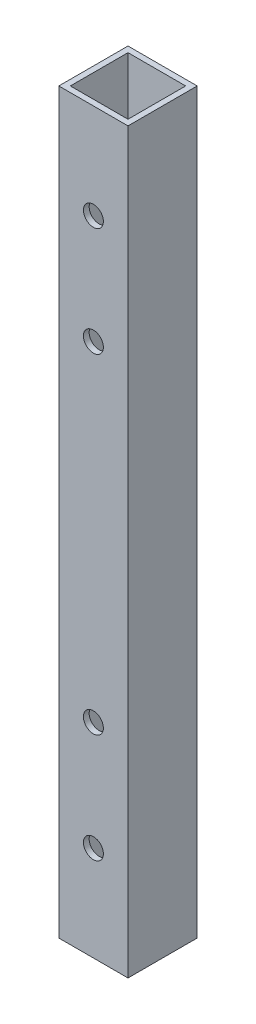
SolidWorks part; units mm, degrees
material "6063-T5"
ref_plane "Front Plane" through (0, 0, 0) normal (0, 0, 1) x (1, 0, 0)
ref_plane "Top Plane" through (0, 0, 0) normal (0, 1, 0) x (1, 0, 0)
ref_plane "Right Plane" through (0, 0, 0) normal (1, 0, 0) x (0, 0, -1)
sketch "Sketch1" plane through (0, 0, 0) normal (0, 1, 0) x (1, 0, 0)
  line L0 (1.5875, 1.5875) -> (17.4625, 1.5875)
  line L5 (0, 0) -> (19.05, 0)
  line L6 (0, 0) -> (0, 19.05)
  line L7 (0, 19.05) -> (19.05, 19.05)
  line L8 (19.05, 0) -> (19.05, 19.05)
  line L9 (17.4625, 1.5875) -> (17.4625, 17.4625)
  line L10 (1.5875, 17.4625) -> (17.4625, 17.4625)
  line L11 (1.5875, 1.5875) -> (1.5875, 17.4625)
  dimension "D1" = 19.05
  dimension "D2" = 19.05
  dimension "D3" = 1.5875
extrude "Boss-Extrude1" add sketch "Sketch1" along normal blind 914.4
sketch "Sketch2" plane through (0, 0, 0) normal (0, 0, 1) x (1, 0, 0)
  line L0 (0, 914.4) -> (19.05, 914.4) construction
  circle A0 centre (9.525, 906.4) radius 2.75
  circle A1 centre (9.525, 891.4) radius 2.75
  dimension "D3" = 5.5
  dimension "D4" = 5.5
  dimension "D1" = 8
  dimension "D2" = 15
extrude "Cut-Extrude1" cut sketch "Sketch2" against normal through all
sketch "Sketch3" plane through (0, 0, -19.05) normal (0, 0, -1) x (-1, 0, 0)
  circle A0 centre (-9.525, 906.4) radius 4.255
  circle A1 centre (-9.525, 891.4) radius 4.255
  dimension "D1" = 8.51
  dimension "D2" = 8.51
extrude "Cut-Extrude2" cut sketch "Sketch3" against normal up to next
sketch "Sketch4" plane through (0, 0, 0) normal (0, 0, 1) x (1, 0, 0)
  line L0 (0, 914.4) -> (0, 0) construction
  line L1 (0, 762) -> (19.05, 762)
  line L2 (0, 762) -> (0, 558.8)
  line L3 (0, 558.8) -> (19.05, 558.8)
  line L4 (19.05, 762) -> (19.05, 558.8)
  line L5 (19.05, 914.4) -> (19.05, 0) construction
  line L6 (0, 914.4) -> (19.05, 914.4) construction
  dimension "D1" = 152.4
  dimension "D2" = 203.2
extrude "Cut-Extrude3" cut sketch "Sketch4" against normal through all flip side to cut
sketch "Sketch5" plane through (0, 0, 0) normal (0, 0, 1) x (1, 0, 0)
  line L0 (19.05, 762) -> (0, 762) construction
  line L1 (19.05, 762) -> (19.05, 558.8) construction
  line L2 (0, 660.4) -> (19.05, 660.4) construction
  line L3 (0, 762) -> (0, 558.8) construction
  circle A0 centre (9.52, 735.8) radius 2.75
  circle A1 centre (9.52, 705.8) radius 2.75
  circle A2 centre (9.52, 585) radius 2.75
  circle A3 centre (9.52, 615) radius 2.75
  dimension "D1" = 5.5
  dimension "D2" = 5.5
  dimension "D3" = 26.2
  dimension "D4" = 56.2
  dimension "D5" = 9.53
  dimension "D6" = 9.53
extrude "Cut-Extrude4" cut sketch "Sketch5" against normal through all
